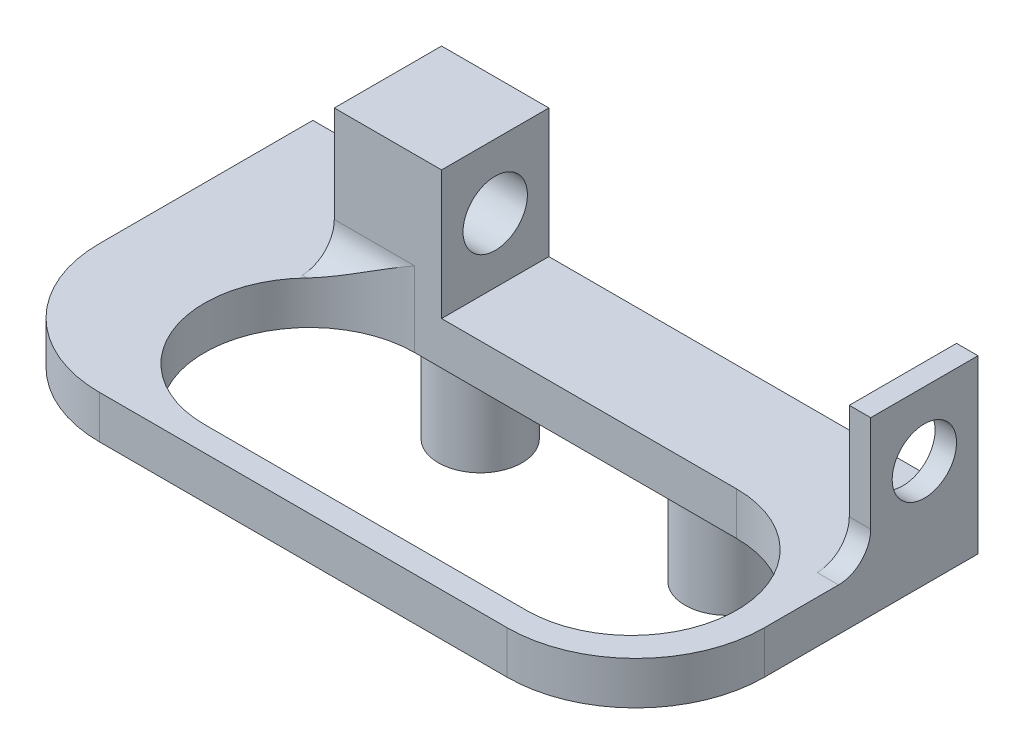
SolidWorks part; units mm, degrees
ref_plane "Front Plane" through (0, 0, 0) normal (0, 0, 1) x (1, 0, 0)
ref_plane "Top Plane" through (0, 0, 0) normal (0, 1, 0) x (1, 0, 0)
ref_plane "Right Plane" through (0, 0, 0) normal (1, 0, 0) x (0, 0, -1)
sketch "Sketch1" plane through (0, 0, 0) normal (0, 1, 0) x (1, 0, 0)
  line L0 (0, 0) -> (11.5, 0) construction
  circle A0 centre (0, 0) radius 1.95
  circle A1 centre (11.5, 0) radius 1.95
extrude "Boss-Extrude2" add sketch "Sketch1" against normal blind 5
sketch "Sketch2" plane through (0, 0, 0) normal (0, 1, 0) x (1, 0, 0)
  line L0 (0, 0) -> (11.5, 0) construction
  line L9 (5.75, 0) -> (21.25, 0) construction
  line L10 (5.75, 0) -> (-9.75, 0) construction
  line L12 (-9.75, 1.95) -> (21.25, 1.95)
  line L13 (-9.75, 1.95) -> (-9.75, -14)
  line L14 (-9.75, -14) -> (21.25, -14)
  line L15 (21.25, 1.95) -> (21.25, -14)
extrude "Boss-Extrude4" add sketch "Sketch2" along normal blind 2
sketch "Sketch3" plane through (0, 0, 0) normal (0, -1, 0) x (1, 0, 0)
  line L0 (0, 1.95) -> (0, 7.95) construction
  line L1 (0, 7.95) -> (15, 7.95) construction
  line L2 (0, 12.85) -> (15, 12.85)
  line L3 (0, 3.05) -> (15, 3.05)
  arc A0 (0, 12.85) -> (0, 3.05) centre (0, 7.95) ccw
  circle A1 centre (0, 0) radius 1.95 construction
  arc A2 (15, 3.05) -> (15, 12.85) centre (15, 7.95) ccw
  point P4 (7.5, 7.95)
extrude "Cut-Extrude1" cut sketch "Sketch3" against normal blind 2
fillet "Fillet1" radius 6 2 edges at (-9.75, 1, 14) (21.25, 1, 14)
sketch "Sketch4" plane through (0, 0, 0) normal (0, -1, 0) x (1, 0, 0)
  line L0 (0, 0) -> (11.5, 0) construction
  line L1 (0, 1.95) -> (11.5, 1.95)
  line L2 (0, -1.95) -> (11.5, -1.95)
  arc A0 (0, 1.95) -> (0, -1.95) centre (0, 0) ccw
  arc A1 (11.5, -1.95) -> (11.5, 1.95) centre (11.5, 0) ccw
  point P4 (5.75, 0)
extrude "Boss-Extrude5" add sketch "Sketch4" along normal blind 1
sketch "Sketch6" plane through (0, 2, 0) normal (0, 1, 0) x (1, 0, 0)
  line L6 (21.25, 1.95) -> (-3.75, 1.95) construction
  line L7 (21.25, 1.95) -> (20.25, 1.95)
  line L8 (21.25, 1.95) -> (21.25, -3.05)
  line L9 (21.25, -3.05) -> (20.25, -3.05)
  line L10 (20.25, 1.95) -> (20.25, -3.05)
  line L11 (21.25, 1.95) -> (-9.75, 1.95) construction
  line L13 (-3.75, 1.95) -> (1.25, 1.95)
  line L14 (-3.75, 1.95) -> (-3.75, -3.05)
  line L15 (-3.75, -3.05) -> (1.25, -3.05)
  line L16 (1.25, 1.95) -> (1.25, -3.05)
extrude "Boss-Extrude6" add sketch "Sketch6" along normal blind 6
sketch "Sketch8" plane through (-3.75, 0, 0) normal (-1, 0, 0) x (0, 0, 1)
  line L0 (0.55, 2) -> (0.55, 5) construction
  line L1 (-1.95, 2) -> (3.05, 2) construction
  circle A0 centre (0.55, 5) radius 1.5
extrude "Cut-Extrude3" cut sketch "Sketch8" against normal through all
fillet "Fillet5" radius 1.5 2 edges at (20.75, 2, 3.05) (-1.875, 2, 3.05)
